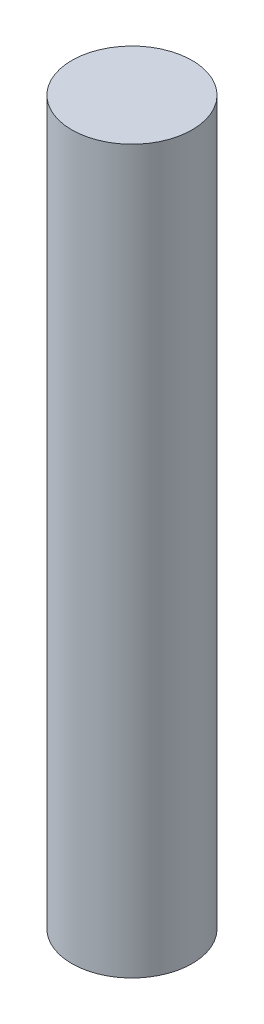
SolidWorks part; units mm, degrees
ref_plane "Front Plane" through (0, 0, 0) normal (0, 0, 1) x (1, 0, 0)
ref_plane "Top Plane" through (0, 0, 0) normal (0, 1, 0) x (1, 0, 0)
ref_plane "Right Plane" through (0, 0, 0) normal (1, 0, 0) x (0, 0, -1)
sketch "Sketch1" plane through (0, 0, 0) normal (0, 1, 0) x (1, 0, 0)
  circle A0 centre (0, 0) radius 12.5
  dimension "D1" = 25
extrude "Boss-Extrude1" add sketch "Sketch1" along normal blind 150
